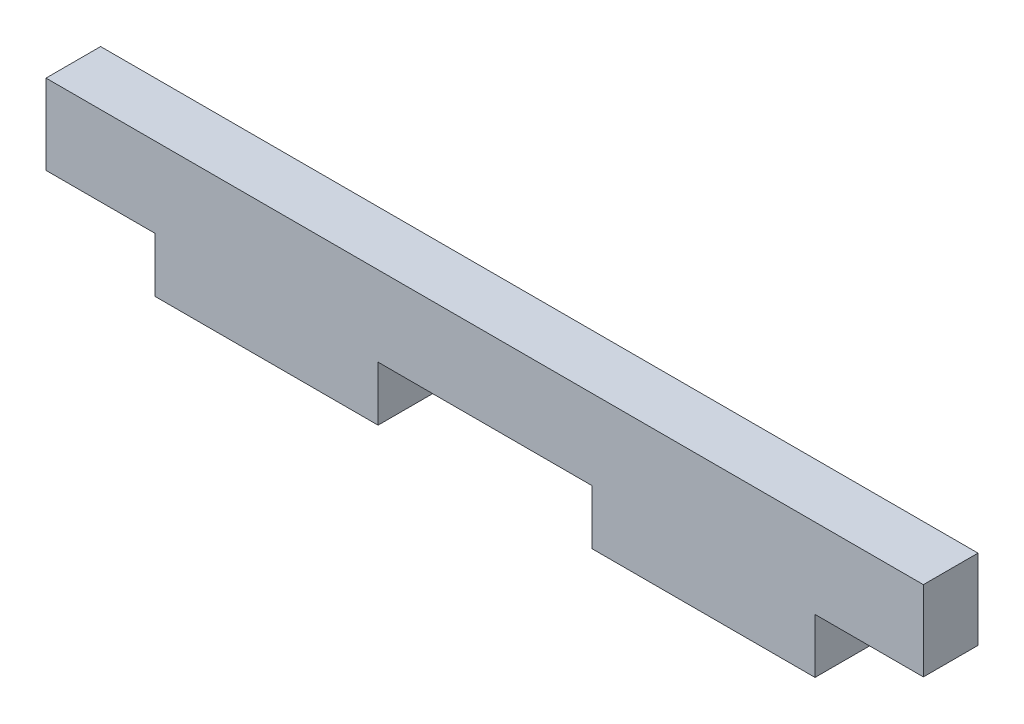
SolidWorks part; units mm, degrees
ref_plane "Front" through (0, 0, 0) normal (0, 0, 1) x (1, 0, 0)
ref_plane "Top" through (0, 0, 0) normal (0, 1, 0) x (1, 0, 0)
ref_plane "Right" through (0, 0, 0) normal (1, 0, 0) x (0, 0, -1)
sketch "Sketch1" plane through (0, 0, 0) normal (0, 0, 1) x (1, 0, 0)
  line L0 (19.2024, -0.7366) -> (25.5016, -0.7366)
  line L1 (25.5016, -0.7366) -> (25.5016, 3.9116)
  line L2 (25.5016, 3.9116) -> (-25.5016, 3.9116)
  line L3 (-25.5016, 3.9116) -> (-25.5016, -0.7366)
  line L4 (-25.5016, -0.7366) -> (-19.1516, -0.7366)
  line L5 (-19.1516, -0.7366) -> (-19.1516, -3.9116)
  line L6 (-19.1516, -3.9116) -> (-6.1976, -3.9116)
  line L7 (-6.1976, -3.9116) -> (-6.1976, -0.7366)
  line L8 (-6.1976, -0.7366) -> (6.2484, -0.7366)
  line L9 (6.2484, -0.7366) -> (6.2484, -3.9116)
  line L10 (6.2484, -3.9116) -> (19.2024, -3.9116)
  line L11 (19.2024, -3.9116) -> (19.2024, -0.7366)
extrude "Boss-Extrude1" add sketch "Sketch1" along normal blind 3.175
